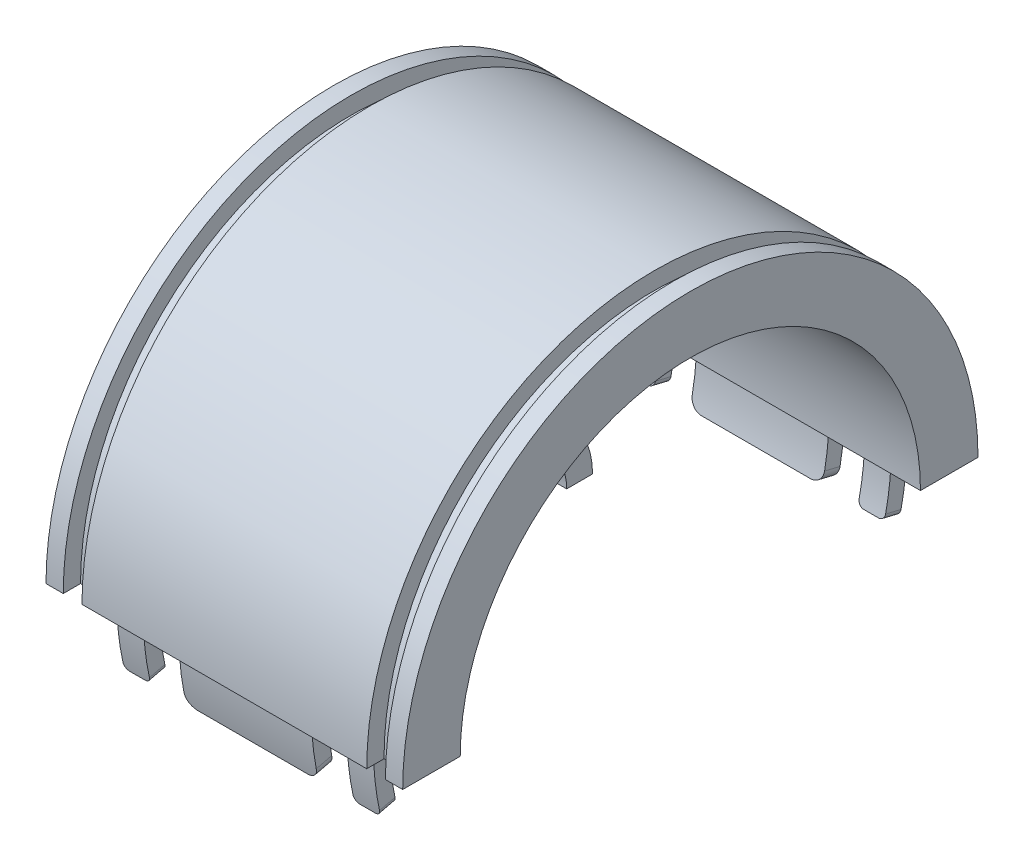
SolidWorks part; units mm, degrees
ref_plane "Front Plane" through (0, 0, 0) normal (0, 0, 1) x (1, 0, 0)
ref_plane "Top Plane" through (0, 0, 0) normal (0, 1, 0) x (1, 0, 0)
ref_plane "Right Plane" through (0, 0, 0) normal (1, 0, 0) x (0, 0, -1)
sketch "Sketch1" plane through (0, 0, 0) normal (0, 1, 0) x (1, 0, 0)
  line L0 (0, 0) -> (155.1991, 0) construction
  line L1 (155.1991, 0) -> (-158.5278, 0) construction
  line L2 (0, 0) -> (0, -90.4212) construction
  line L3 (0, 0) -> (0, 195.4795) construction
  line L9 (24.75, 47) -> (28, 47)
  line L10 (31, 50) -> (28, 50)
  line L15 (31, 50) -> (31, 40)
  line L16 (31, 40) -> (-26, 40)
  line L22 (-31, 50) -> (-31, 40)
  line L23 (31, 50) -> (28, 49.5161) construction
  line L24 (31, 40) -> (-24.75, 48.9919) construction
  line L26 (-24.75, 50) -> (-24.75, 47)
  line L27 (-24.75, 47) -> (-28, 47)
  line L28 (-28, 50) -> (-28, 47)
  line L29 (24.75, 50) -> (-24.75, 50)
  line L30 (24.75, 48.9919) -> (-26, 40.8065) construction
  line L35 (28, 50) -> (28, 47)
  line L36 (24.75, 50) -> (24.75, 47)
  line L38 (-28, 50) -> (-31, 50)
  line L39 (-28, 49.5161) -> (-31, 50) construction
  line L40 (-26, 77.8545) -> (-26, 16.5) construction
  line L41 (-35, 76.0219) -> (-35, -31.7141) construction
  line L42 (-31, 40) -> (-31, -27.11) construction
  line L43 (-97.0302, 16.5) -> (67.6651, 16.5) construction
  line L44 (-97.0302, 14) -> (77.1364, 14) construction
  line L45 (-85.0595, 9.5) -> (85.95, 9.5) construction
  line L46 (-80.3239, 27.25) -> (68.7175, 27.25) construction
  line L47 (-10, 63.6566) -> (-10, -23.2952) construction
  line L48 (-28, 68.9882) -> (-28, -37.4297) construction
  line L49 (-24.75, 67.96) -> (-24.75, -40.5143) construction
  line L50 (-18.153, 23.85) -> (-54.2967, 23.85) construction
  line L51 (-18.153, 18.7) -> (-49.456, 18.7) construction
  line L52 (-9.9469, 14) -> (-10, 9.5)
  spline S0 degree 3 poles (-31, 40) (-32.9396, 37.5406) (-36.9339, 27.5823) (-30.0824, 11.7757) (-17.9219, 9.5) (-10, 9.5) knots 0 0 0 0 0.268185 0.444495 0.82256 0.82256 0.82256 0.82256
  spline S1 degree 3 poles (-26, 40) (-27.0137, 36.8092) (-29.3451, 27.8281) (-24.5235, 15.3947) (-15.5263, 14.8685) (-9.9469, 14) knots 0 0 0 0 0.285239 0.456571 0.779818 0.779818 0.779818 0.779818
  point P3 (0, 45)
  point P11 (-26.375, 50)
  dimension "D14" = 3
  dimension "D1" = 62
  dimension "D2" = 10
  dimension "D3" = 50
  dimension "D4" = 3
  dimension "D5" = 3
  dimension "D6" = 5
  dimension "D7" = 4
  dimension "D8" = 23.5
  dimension "D9" = 26
  dimension "D10" = 30.5
  dimension "D11" = 12.75
  dimension "D12" = 21
  dimension "D13" = 10
  dimension "D15" = 6.25
  dimension "D16" = 16.15
  dimension "D17" = 21.3
revolve "Revolve1" add sketch "Sketch1" angle 180 about L0
ref_plane "Plane1" through (0, 0, 0) normal (0, -1, 0) x (-1, 0, 0)
sketch "Sketch2" plane through (0, 0, 0) normal (0, -1, 0) x (-1, 0, 0)
  line L0 (0, 0) -> (0, -63.4772) construction
  line L1 (0, -63.4772) -> (0, 65.8935) construction
  line L2 (0, 0) -> (-92.8791, 0) construction
  line L3 (-92.8791, 0) -> (91.2198, 0) construction
  line L4 (-11.5, -45) -> (11.5, -45) construction
  line L5 (11.5, -46.38) -> (-11.5, -46.38)
  line L6 (11.5, -46.38) -> (11.5, -43.62)
  line L7 (11.5, -43.62) -> (-11.5, -43.62)
  line L8 (-11.5, -46.38) -> (-11.5, -43.62)
  line L9 (22.3, -43.62) -> (17.7, -43.62)
  line L10 (-22.3, -43.62) -> (-17.7, -43.62)
  line L11 (-22.3, -43.62) -> (-22.3, -46.38)
  line L12 (-22.3, -46.38) -> (-17.7, -46.38)
  line L13 (-17.7, -43.62) -> (-17.7, -46.38)
  line L14 (22.3, -43.62) -> (22.3, -46.38)
  line L15 (22.3, -46.38) -> (17.7, -46.38)
  line L16 (17.7, -43.62) -> (17.7, -46.38)
  line L17 (-20, -43.62) -> (-20, -63.3325) construction
  line L18 (-22.3, -45) -> (37.0527, -45) construction
  line L19 (-31, -45) -> (51.3033, -45) construction
  line L20 (-31, -40) -> (-31, -50) construction
  dimension "D1" = 11.5
  dimension "D2" = 11.5
  dimension "D3" = 2.76
  dimension "D5" = 4.6
  dimension "D6" = 2.76
  dimension "D7" = 20
revolve "Revolve2" add sketch "Sketch2" angle 13.5 about L2
fillet "Fillet1" radius 2 2 edges at (11.5, -10.505, 43.7566) (-11.5, -10.505, 43.7566)
mirror "Mirror4" about plane through (0, 0, 0) normal (0, 0, 1) of "Revolve2"
fillet "Fillet3" radius 2 2 edges at (-11.5, -10.505, -43.7566) (11.5, -10.505, -43.7566)
sketch "Sketch6" plane through (0, 0, 0) normal (1, 0, 0) x (0, 0, -1)
  line L0 (-29.6412, 0) -> (65.6482, 0) construction
  line L1 (37.3637, 0) -> (-37.3637, 0) construction
  line L2 (-14, 0) -> (-9.5, 0)
  line L3 (9.5, 0) -> (14, 0)
  arc A0 (9.5, 0) -> (-9.5, 0) centre (0, 0) ccw
  arc A1 (14, 0) -> (-14, 0) centre (0, 0) ccw
extrude "Boss-Extrude1" add sketch "Sketch6" against normal up to surface (31 mm away) up to face at (-31, 22.5, 0)
ref_plane "Plane3" through (31, 0, 0) normal (1, 0, 0) x (0, 0, -1)
sketch "Sketch7" plane through (31, 0, 0) normal (1, 0, 0) x (0, 0, -1)
  line L0 (4.7883, 13.1557) -> (13.6808, 37.5877)
  line L1 (-4.7883, 13.1557) -> (-13.6808, 37.5877)
  line L2 (0, 27.5) -> (0, -27.5) construction
  arc A0 (4.7883, 13.1557) -> (-4.7883, 13.1557) centre (0, 0) ccw
  arc A1 (13.6808, 37.5877) -> (-13.6808, 37.5877) centre (0, 0) ccw
  dimension "D1" = 20
  dimension "D2" = 20
extrude "Cut-Extrude2" cut sketch "Sketch7" against normal blind 74
pattern_circular "CirPattern2" count 6 over 360 about axis through (0, 0, 0) along (1, 0, 0) of "Cut-Extrude2"
fillet "Fillet4" radius 1 8 edges at (-17.7, -10.505, -43.7566) (-22.3, -10.505, -43.7566) (17.7, -10.505, -43.7566) (22.3, -10.505, -43.7566) (-17.7, -10.505, 43.7566) (-22.3, -10.505, 43.7566) (17.7, -10.505, 43.7566) (22.3, -10.505, 43.7566)
